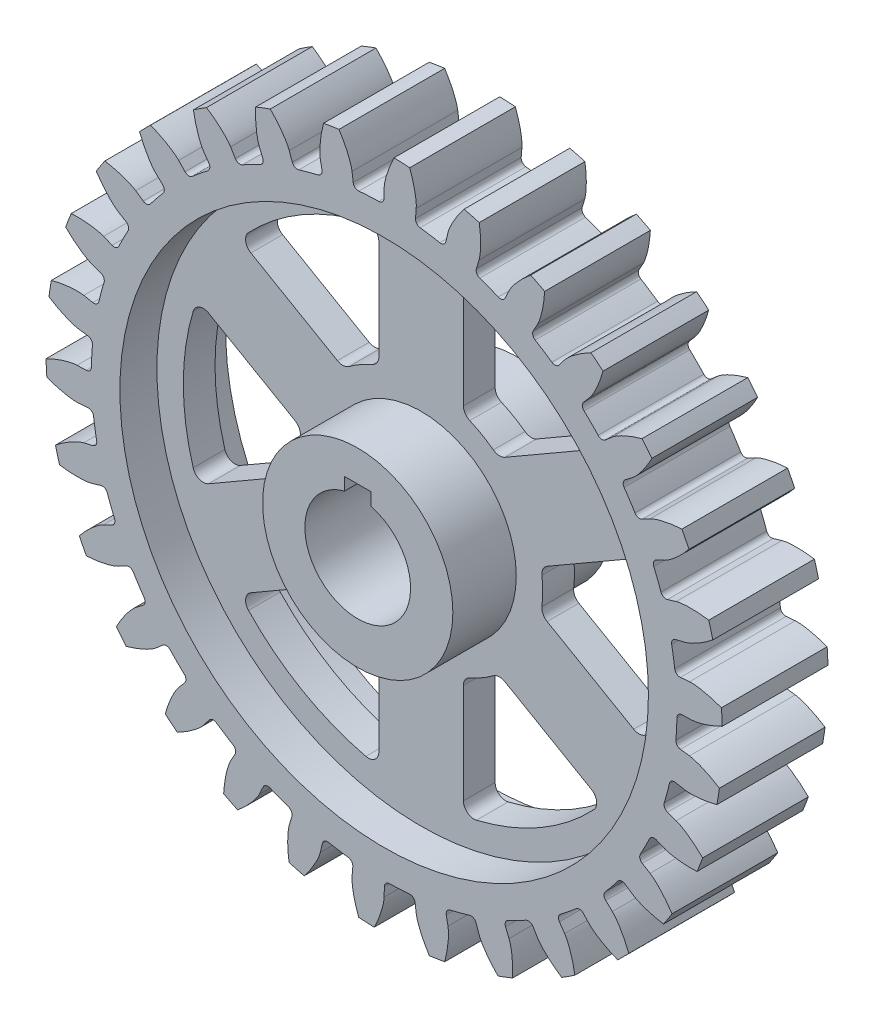
SolidWorks part; units mm, degrees
ref_plane "Front Plane" through (0, 0, 0) normal (0, 0, 1) x (1, 0, 0)
ref_plane "Top Plane" through (0, 0, 0) normal (0, 1, 0) x (1, 0, 0)
ref_plane "Right Plane" through (0, 0, 0) normal (1, 0, 0) x (0, 0, -1)
sketch "Sketch1" plane through (0, 0, 0) normal (1, 0, 0) x (0, 0, -1)
  line L0 (-19.05, 0) -> (19.05, 0)
  line L1 (10.4775, 0) -> (-10.4775, 0) construction
  line L2 (19.05, 0) -> (19.05, 22.86)
  line L3 (19.05, 22.86) -> (3.81, 22.86)
  line L4 (3.81, 22.86) -> (3.81, 63.5)
  line L5 (3.81, 63.5) -> (12.7, 63.5)
  line L6 (12.7, 63.5) -> (12.7, 70.358)
  line L7 (12.7, 70.358) -> (-12.7, 70.358)
  line L8 (0, 38.6969) -> (0, -38.6969) construction
  line L9 (0, 70.358) -> (0, 0) construction
  line L10 (-19.05, 0) -> (-19.05, 22.86)
  line L11 (-19.05, 22.86) -> (-3.81, 22.86)
  line L12 (-3.81, 22.86) -> (-3.81, 63.5)
  line L13 (-3.81, 63.5) -> (-12.7, 63.5)
  line L14 (-12.7, 63.5) -> (-12.7, 70.358)
  point P16 (0, 0)
  point P21 (0, 70.358)
  dimension "D1" = 19.05
  dimension "D2" = 22.86
  dimension "D3" = 3.81
  dimension "D4" = 63.5
  dimension "D5" = 70.358
  dimension "D6" = 12.7
ref_axis "Axis1" through (0, 0, 20.955) along (0, 0, -1)
revolve "Revolve2" add sketch "Sketch1" angle 360 about axis through (0, 0, 20.955) along (0, 0, -1)
sketch "Sketch2" plane through (0, 0, 0) normal (0, 0, 1) x (1, 0, 0)
  line L0 (73.787, -0.0004) -> (70.358, -0.0729)
  line L1 (0, 0) -> (190.3085, 9.9736) construction
  line L2 (73.3828, 7.7128) -> (69.9649, 7.4269)
  arc A0 (81.2453, 2.3731) -> (81.0484, 6.132) centre (0, 0) ccw
  circle A3 centre (0, 0) radius 70.358 construction
  arc A4 (70.358, -0.0729) -> (69.9649, 7.4269) centre (0, 0) ccw
  spline S0 degree 4 poles (73.787, -0.0004) (73.8416, 0.0008) (73.9944, 0.0076) (74.2828, 0.0346) (74.7515, 0.0986) (75.345, 0.2093) (76.1065, 0.3857) (76.995, 0.6361) (77.9608, 0.9555) (78.9981, 1.35) (80.0202, 1.7851) (81.0261, 2.2564) (82.0158, 2.7607) (83.1972, 3.4094) (84.592, 4.2446) (86.1811, 5.2928) (87.9419, 6.5805) (89.6733, 7.973) (91.3432, 9.4387) (92.7509, 10.7793) (93.9201, 11.9666) (94.8691, 12.9794) (95.614, 13.8041) (96.5255, 14.8496) (97.4145, 15.9194) (98.1892, 16.8945) (98.8659, 17.782) (99.3591, 18.4419) (99.8613, 19.1325) (100.322, 19.7789) (100.825, 20.5112) (101.2453, 21.1304) (101.7679, 21.9261) (102.1191, 22.4718) (102.7346, 23.4526) (103.1421, 24.1295) (103.5488, 24.81) (103.7468, 25.1566) (103.8765, 25.3795) knots 0 0 0 0 0 0.005377 0.015084 0.028532 0.04661 0.064855 0.092111 0.119476 0.146842 0.174209 0.201575 0.228941 0.256307 0.307035 0.361767 0.4165 0.471232 0.525964 0.580697 0.608063 0.635429 0.662795 0.690161 0.744894 0.77226 0.785943 0.799626 0.826992 0.854358 0.868042 0.881725 0.909091 0.931818 0.954545 0.977273 1 1 1 1 1 construction
  spline S1 degree 4 poles (73.787, -0.0004) (73.8416, 0.0008) (73.9944, 0.0076) (74.2828, 0.0346) (74.7515, 0.0986) (75.345, 0.2093) (76.1065, 0.3857) (76.995, 0.6361) (77.9608, 0.9555) (78.9981, 1.35) (79.9496, 1.755) (80.6355, 2.0737) (81.0655, 2.2836) (81.2453, 2.3731) knots 0 0 0 0 0 0.005377 0.015084 0.028532 0.04661 0.064855 0.092111 0.119476 0.146842 0.174209 0.194009 0.194009 0.194009 0.194009 0.194009
  spline S2 degree 4 poles (73.3828, 7.7128) (73.4372, 7.7174) (73.5899, 7.7266) (73.8795, 7.7299) (74.3523, 7.7153) (74.9541, 7.6672) (75.7299, 7.5713) (76.6397, 7.4152) (77.6336, 7.1984) (78.7065, 6.9146) (79.6951, 6.6113) (80.4105, 6.366) (80.8602, 6.2022) (81.0484, 6.132) knots 0 0 0 0 0 0.005377 0.015084 0.028532 0.04661 0.064855 0.092111 0.119476 0.146842 0.174209 0.194009 0.194009 0.194009 0.194009 0.194009
  point P5 (70.358, -0.0729)
  point P9 (0, 0)
  dimension "D1" = 162.56
extrude "Boss-Extrude2" add sketch "Sketch2" along normal blind 12.7 and the other way blind 12.7
fillet "Fillet5" radius 1.27 1 edges at (69.9649, 7.4269, 0)
fillet "Fillet6" radius 1.27 1 edges at (70.358, -0.0729, 0)
pattern_circular "CirPattern1" count 30 over 360 about axis through (0, 0, 20.955) along (0, 0, -1) of "Boss-Extrude2", "Fillet5", "Fillet6"
sketch "Sketch3" plane through (0, 0, 0) normal (0, 0, 1) x (1, 0, 0)
  line L2 (-3.175, 12.2967) -> (-3.175, 15.3447)
  line L3 (-3.175, 15.3447) -> (3.175, 15.3447)
  line L4 (3.175, 12.2967) -> (3.175, 15.3447)
  arc A0 (-3.175, 12.2967) -> (3.175, 12.2967) centre (0, 0) ccw
  point P7 (0, 0)
  dimension "D1" = 6.35
  dimension "D2" = 25.4
  dimension "D3" = 3.175
  dimension "D4" = 3.048
extrude "Cut-Extrude1" cut sketch "Sketch3" against normal through all both and the other way through all
sketch "Sketch4" plane through (0, 0, 0) normal (0, 0, 1) x (1, 0, 0)
  line L0 (10.16, 27.3861) -> (10.16, 56.2396)
  line L2 (0, -20.955) -> (0, 20.955) construction
  line L3 (0, 0) -> (81.8114, 47.2338) construction
  line L4 (18.6371, 22.4919) -> (43.625, 36.9186)
  line L5 (20.955, 0) -> (-20.955, 0) construction
  arc A0 (43.625, 36.9186) -> (10.16, 56.2396) centre (0, 0) ccw
  arc A1 (18.6371, 22.4919) -> (10.16, 27.3861) centre (0, 0) ccw
  dimension "D3" = 29.21
  dimension "D4" = 57.15
  dimension "D1" = 10.16
  dimension "D2" = 10.16
  dimension "D5" = 30
extrude "Cut-Extrude2" cut sketch "Sketch4" against normal through all both and the other way through all
fillet "Fillet7" radius 2.54 4 edges at (43.625, 36.9186, 0) (10.16, 56.2396, 0) (18.6371, 22.4919, 0) (10.16, 27.3861, 0)
pattern_circular "CirPattern2" count 6 over 360 about axis through (0, 0, 0) along (0, 0, 1) of "Cut-Extrude2", "Fillet7"
